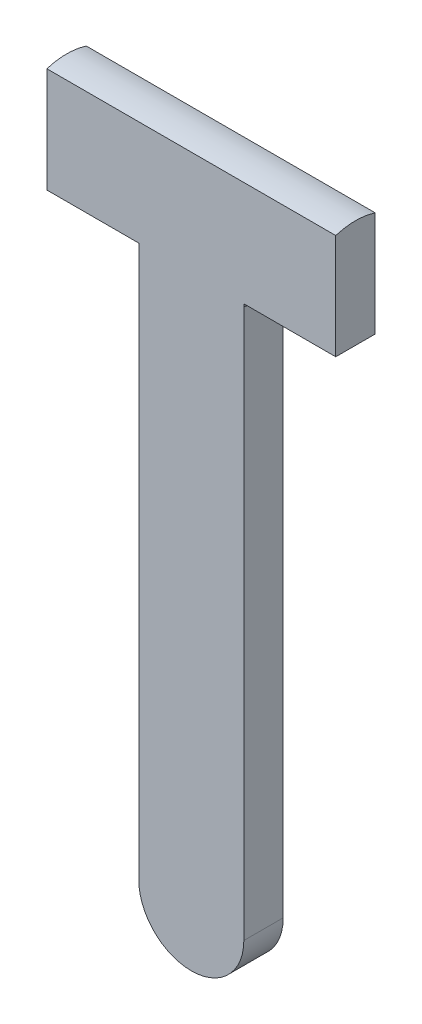
SolidWorks part; units mm, degrees
ref_plane "Face" through (0, 0, 0) normal (0, 0, 1) x (1, 0, 0)
ref_plane "Dessus" through (0, 0, 0) normal (0, 1, 0) x (1, 0, 0)
ref_plane "Droite" through (0, 0, 0) normal (1, 0, 0) x (0, 0, -1)
sketch "Esquisse1" plane through (0, 0, 0) normal (0, 0, 1) x (1, 0, 0)
  line L0 (-5.5, 0) -> (5.5, 0)
  line L1 (-5.5, -4) -> (-2, -4)
  line L2 (0, 0) -> (0, -33.6958) construction
  line L3 (-5.5, 0) -> (-5.5, -4)
  line L5 (5.5, -4) -> (5.5, 0)
  line L6 (2, -4) -> (5.5, -4)
  line L8 (-2, -4) -> (-2, -25)
  line L10 (2, -4) -> (2, -25)
  arc A0 (-2, -25) -> (2, -25) centre (0, -25) ccw
  dimension "D5" = 25
  dimension "D1" = 4
  dimension "D2" = 11
  dimension "D3" = 4
  dimension "D4" = 3.5
  dimension "D6" = 11
extrude "Extrusion1" add sketch "Esquisse1" along normal blind 1.5
sketch "Esquisse2" plane through (0, -4, 0) normal (0, -1, 0) x (1, 0, 0)
  line L1 (-2, 1.5) -> (-2, 0) construction
  line L3 (-2, 1.5) -> (-2, 0)
  line L4 (2, 1.5) -> (2, 0) construction
  line L5 (2, 1.5) -> (2, 0)
  arc A0 (-2, 1.5) -> (-2, 0) centre (0, 0.75) ccw
  arc A1 (2, 0) -> (2, 1.5) centre (0, 0.75) ccw
extrude "Extrusion2" add sketch "Esquisse2" along normal blind 0.1
sketch "Esquisse3" plane through (-5.5, 0, 0) normal (-1, 0, 0) x (0, 0, 1)
  line L0 (1.5, 0) -> (0, 0) construction
  line L1 (1.5, 0) -> (0, 0)
  arc A0 (1.5, 0) -> (0, 0) centre (0.75, -2.3848) ccw
  dimension "D1" = 5
extrude "Extrusion3" add sketch "Esquisse3" against normal up to surface (11 mm away) up to face at (5.5, -2, 0.75)
